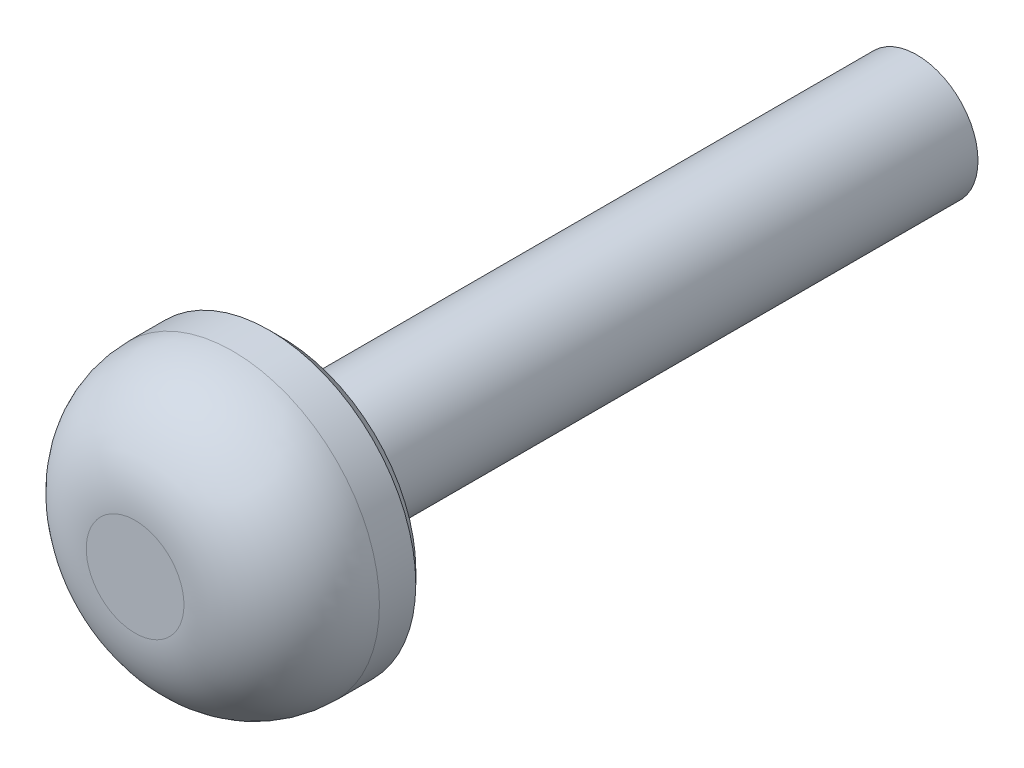
SolidWorks part; units mm, degrees
ref_plane "Front Plane" through (0, 0, 0) normal (0, 0, 1) x (1, 0, 0)
ref_plane "Top Plane" through (0, 0, 0) normal (0, 1, 0) x (1, 0, 0)
ref_plane "Right Plane" through (0, 0, 0) normal (1, 0, 0) x (0, 0, -1)
sketch "Sketch1" plane through (0, 0, 0) normal (0, 0, 1) x (1, 0, 0)
  circle A0 centre (0, 0) radius 1.25
  dimension "D1" = 2.5
extrude "Boss-Extrude1" add sketch "Sketch1" along normal blind 16
sketch "Sketch2" plane through (0, 0, 16) normal (0, 0, 1) x (1, 0, 0)
  circle A0 centre (0, 0) radius 3
  dimension "D1" = 6
extrude "Boss-Extrude2" add sketch "Sketch2" against normal blind 3
fillet "Fillet1" radius 2 1 edges at (3, 0, 16)
chamfer "Chamfer1" distance 0.256 angle 45 1 edges at (3, 0, 13)
